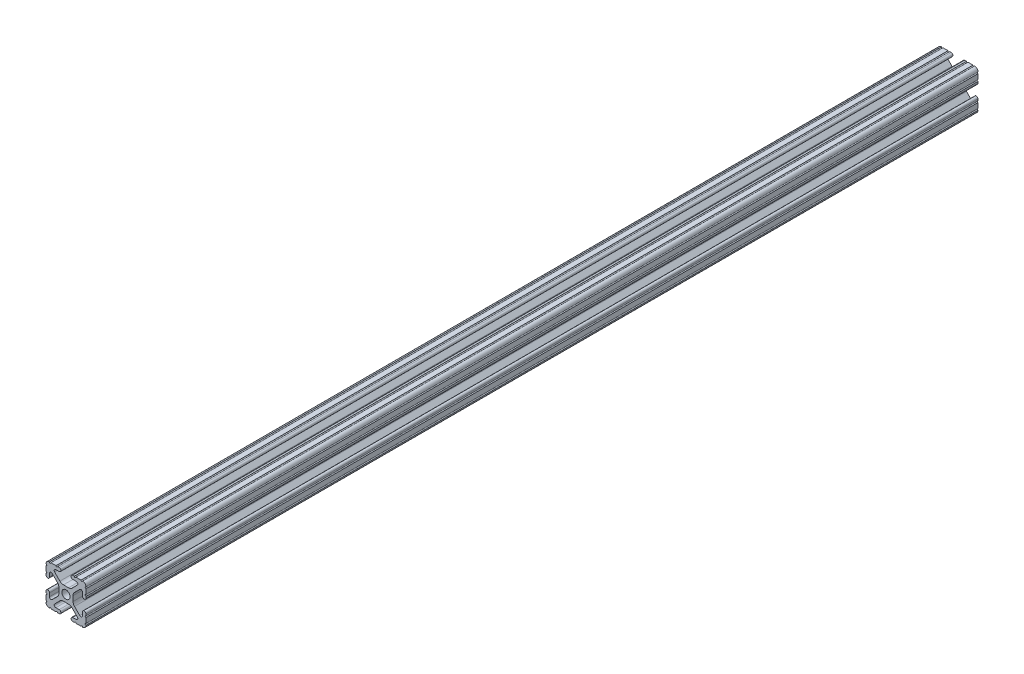
SolidWorks part; units mm, degrees
ref_plane "Front Plane" through (0, 0, 0) normal (0, 0, 1) x (1, 0, 0)
ref_plane "Top Plane" through (0, 0, 0) normal (0, 1, 0) x (1, 0, 0)
ref_plane "Right Plane" through (0, 0, 0) normal (1, 0, 0) x (0, 0, -1)
sketch "Sketch1" plane through (0, 0, 0) normal (0, 0, 1) x (1, 0, 0)
  line L0 (-12.7, -6.3331) -> (-12.7, -9.5504)
  line L1 (-9.5504, -12.7) -> (-6.3331, -12.7)
  line L2 (-5.3171, -12.7) -> (-4.3434, -12.7)
  line L3 (-4.3434, -10.4902) -> (-6.4748, -10.4902)
  line L4 (-7.1932, -8.7558) -> (-3.8632, -5.4257)
  line L5 (-1.6181, -4.4958) -> (1.6181, -4.4958)
  line L6 (3.8632, -5.4257) -> (7.1932, -8.7558)
  line L7 (6.4748, -10.4902) -> (4.3434, -10.4902)
  line L8 (4.3434, -12.7) -> (5.3171, -12.7)
  line L9 (6.3331, -12.7) -> (9.5504, -12.7)
  line L10 (12.7, -9.5504) -> (12.7, -6.3331)
  line L11 (12.7, -5.3171) -> (12.7, -4.3434)
  line L12 (10.4902, -4.3434) -> (10.4902, -6.4748)
  line L13 (8.7558, -7.1932) -> (5.4257, -3.8632)
  line L14 (4.4958, -1.6181) -> (4.4958, 1.6181)
  line L15 (5.4257, 3.8632) -> (8.7558, 7.1932)
  line L16 (10.4902, 6.4748) -> (10.4902, 4.3434)
  line L17 (12.7, 4.3434) -> (12.7, 5.3171)
  line L18 (12.7, 6.3331) -> (12.7, 9.5504)
  line L19 (9.5504, 12.7) -> (6.3331, 12.7)
  line L20 (5.3171, 12.7) -> (4.3434, 12.7)
  line L21 (4.3434, 10.4902) -> (6.4748, 10.4902)
  line L22 (7.1932, 8.7558) -> (3.8632, 5.4257)
  line L23 (1.6181, 4.4958) -> (-1.6181, 4.4958)
  line L24 (-3.8632, 5.4257) -> (-7.1932, 8.7558)
  line L25 (-6.4748, 10.4902) -> (-4.3434, 10.4902)
  line L26 (-4.3434, 12.7) -> (-5.3171, 12.7)
  line L27 (-6.3331, 12.7) -> (-9.5504, 12.7)
  line L28 (-12.7, 9.5504) -> (-12.7, 6.3331)
  line L29 (-12.7, 5.3171) -> (-12.7, 4.3434)
  line L30 (-10.4902, 4.3434) -> (-10.4902, 6.4748)
  line L31 (-8.7558, 7.1932) -> (-5.4257, 3.8632)
  line L32 (-4.4958, 1.6181) -> (-4.4958, -1.6181)
  line L33 (-5.4257, -3.8632) -> (-8.7558, -7.1932)
  line L34 (-10.4902, -6.4748) -> (-10.4902, -4.3434)
  line L35 (-12.7, -4.3434) -> (-12.7, -5.3171)
  circle A0 centre (0, 0) radius 2.6035
  arc A1 (-12.7, -5.3171) -> (-12.7, -6.3331) centre (-12.7, -5.8251) cw
  arc A2 (-12.7, -9.5504) -> (-12.6998, -10.5664) centre (-12.7, -10.0584) cw
  arc A3 (-12.6998, -10.5664) -> (-10.5664, -12.6998) centre (-10.5918, -10.5918) ccw
  arc A4 (-10.5664, -12.6998) -> (-9.5504, -12.7) centre (-10.0584, -12.7) cw
  arc A5 (-6.3331, -12.7) -> (-5.3171, -12.7) centre (-5.8251, -12.7) cw
  arc A6 (-4.3434, -12.7) -> (-4.3434, -10.4902) centre (-4.3434, -11.5951) ccw
  arc A7 (-6.4748, -10.4902) -> (-7.1932, -8.7558) centre (-6.4748, -9.4742) cw
  arc A8 (-3.8632, -5.4257) -> (-1.6181, -4.4958) centre (-1.6181, -7.6708) cw
  arc A9 (1.6181, -4.4958) -> (3.8632, -5.4257) centre (1.6181, -7.6708) cw
  arc A10 (7.1932, -8.7558) -> (6.4748, -10.4902) centre (6.4748, -9.4742) cw
  arc A11 (4.3434, -10.4902) -> (4.3434, -12.7) centre (4.3434, -11.5951) ccw
  arc A12 (5.3171, -12.7) -> (6.3331, -12.7) centre (5.8251, -12.7) cw
  arc A13 (9.5504, -12.7) -> (10.5664, -12.6998) centre (10.0584, -12.7) cw
  arc A14 (10.5664, -12.6998) -> (12.6998, -10.5664) centre (10.5918, -10.5918) ccw
  arc A15 (12.6998, -10.5664) -> (12.7, -9.5504) centre (12.7, -10.0584) cw
  arc A16 (12.7, -6.3331) -> (12.7, -5.3171) centre (12.7, -5.8251) cw
  arc A17 (12.7, -4.3434) -> (10.4902, -4.3434) centre (11.5951, -4.3434) ccw
  arc A18 (10.4902, -6.4748) -> (8.7558, -7.1932) centre (9.4742, -6.4748) cw
  arc A19 (5.4257, -3.8632) -> (4.4958, -1.6181) centre (7.6708, -1.6181) cw
  arc A20 (4.4958, 1.6181) -> (5.4257, 3.8632) centre (7.6708, 1.6181) cw
  arc A21 (8.7558, 7.1932) -> (10.4902, 6.4748) centre (9.4742, 6.4748) cw
  arc A22 (10.4902, 4.3434) -> (12.7, 4.3434) centre (11.5951, 4.3434) ccw
  arc A23 (12.7, 5.3171) -> (12.7, 6.3331) centre (12.7, 5.8251) cw
  arc A24 (12.7, 9.5504) -> (12.6998, 10.5664) centre (12.7, 10.0584) cw
  arc A25 (12.6998, 10.5664) -> (10.5664, 12.6998) centre (10.5918, 10.5918) ccw
  arc A26 (10.5664, 12.6998) -> (9.5504, 12.7) centre (10.0584, 12.7) cw
  arc A27 (6.3331, 12.7) -> (5.3171, 12.7) centre (5.8251, 12.7) cw
  arc A28 (4.3434, 12.7) -> (4.3434, 10.4902) centre (4.3434, 11.5951) ccw
  arc A29 (6.4748, 10.4902) -> (7.1932, 8.7558) centre (6.4748, 9.4742) cw
  arc A30 (3.8632, 5.4257) -> (1.6181, 4.4958) centre (1.6181, 7.6708) cw
  arc A31 (-1.6181, 4.4958) -> (-3.8632, 5.4257) centre (-1.6181, 7.6708) cw
  arc A32 (-7.1932, 8.7558) -> (-6.4748, 10.4902) centre (-6.4748, 9.4742) cw
  arc A33 (-4.3434, 10.4902) -> (-4.3434, 12.7) centre (-4.3434, 11.5951) ccw
  arc A34 (-5.3171, 12.7) -> (-6.3331, 12.7) centre (-5.8251, 12.7) cw
  arc A35 (-9.5504, 12.7) -> (-10.5664, 12.6998) centre (-10.0584, 12.7) cw
  arc A36 (-10.5664, 12.6998) -> (-12.6998, 10.5664) centre (-10.5918, 10.5918) ccw
  arc A37 (-12.6998, 10.5664) -> (-12.7, 9.5504) centre (-12.7, 10.0584) cw
  arc A38 (-12.7, 6.3331) -> (-12.7, 5.3171) centre (-12.7, 5.8251) cw
  arc A39 (-12.7, 4.3434) -> (-10.4902, 4.3434) centre (-11.5951, 4.3434) ccw
  arc A40 (-10.4902, 6.4748) -> (-8.7558, 7.1932) centre (-9.4742, 6.4748) cw
  arc A41 (-5.4257, 3.8632) -> (-4.4958, 1.6181) centre (-7.6708, 1.6181) cw
  arc A42 (-4.4958, -1.6181) -> (-5.4257, -3.8632) centre (-7.6708, -1.6181) cw
  arc A43 (-8.7558, -7.1932) -> (-10.4902, -6.4748) centre (-9.4742, -6.4748) cw
  arc A44 (-10.4902, -4.3434) -> (-12.7, -4.3434) centre (-11.5951, -4.3434) ccw
extrude "Boss-Extrude1" add sketch "Sketch1" against normal blind 566.7375
